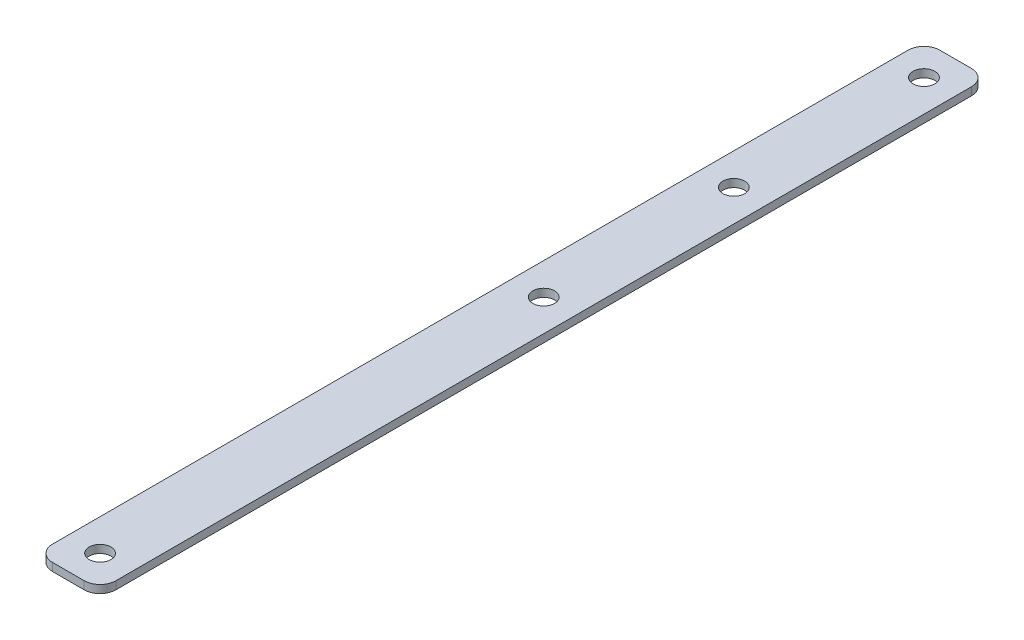
SolidWorks part; units mm, degrees
ref_plane "Front Plane" through (0, 0, 0) normal (0, 0, 1) x (1, 0, 0)
ref_plane "Top Plane" through (0, 0, 0) normal (0, 1, 0) x (1, 0, 0)
ref_plane "Right Plane" through (0, 0, 0) normal (1, 0, 0) x (0, 0, -1)
sketch "Sketch1" plane through (0, 0, 0) normal (0, 1, 0) x (1, 0, 0)
  line L1 (3.175, 0) -> (9.525, 0)
  line L2 (0, 3.175) -> (0, 174.625)
  line L3 (3.175, 177.8) -> (9.525, 177.8)
  line L4 (12.7, 3.175) -> (12.7, 174.625)
  arc A0 (3.175, 177.8) -> (0, 174.625) centre (3.175, 174.625) ccw
  arc A1 (12.7, 174.625) -> (9.525, 177.8) centre (9.525, 174.625) ccw
  arc A2 (3.175, 0) -> (0, 3.175) centre (3.175, 3.175) cw
  arc A3 (12.7, 3.175) -> (9.525, 0) centre (9.525, 3.175) cw
  circle A4 centre (6.35, 171.45) radius 2.1828
  circle A5 centre (6.35, 6.35) radius 2.1828
  circle A6 centre (6.35, 133.35) radius 2.1828
  circle A7 centre (6.35, 95.25) radius 2.1828
  point P11 (0, 0)
  point P14 (12.7, 0)
  dimension "D3" = 3.175
  dimension "D4" = 3.175
  dimension "D5" = 3.175
  dimension "D6" = 3.175
  dimension "D9" = 4.3656
  dimension "D12" = 4.3656
  dimension "D13" = 4.3656
  dimension "D16" = 4.3656
  dimension "D1" = 12.7
  dimension "D2" = 177.8
  dimension "D7" = 6.35
  dimension "D8" = 6.35
  dimension "D10" = 6.35
  dimension "D11" = 6.35
  dimension "D14" = 6.35
  dimension "D15" = 38.1
  dimension "D17" = 6.35
  dimension "D18" = 38.1
extrude "Boss-Extrude1" add sketch "Sketch1" along normal blind 1.5875
